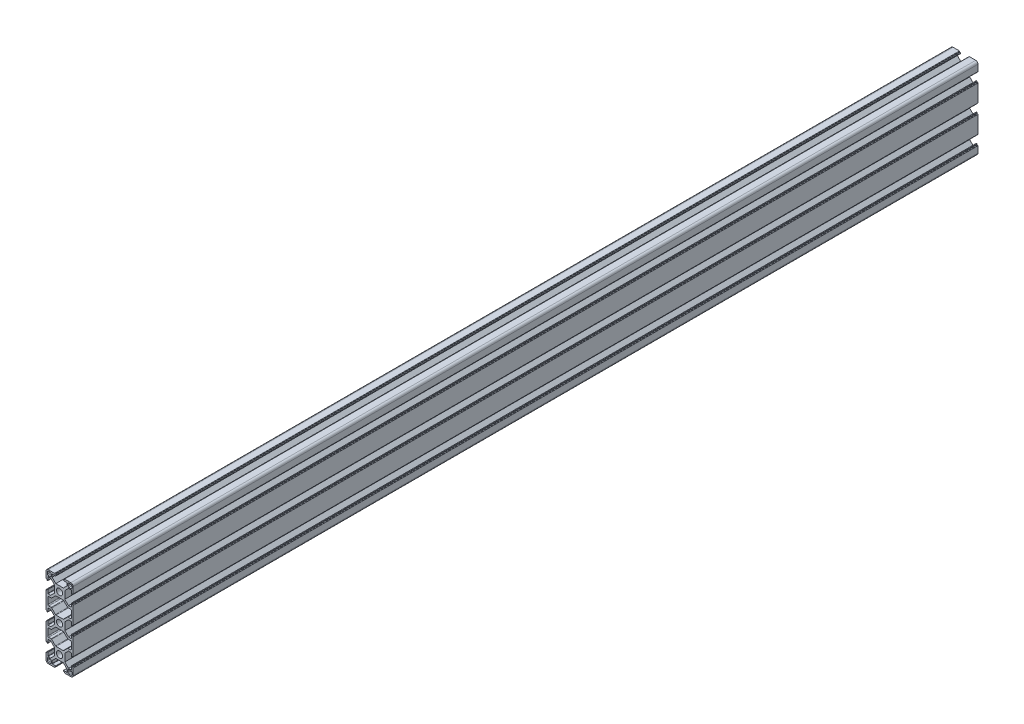
SolidWorks part; units mm, degrees
material "6063 T5"
ref_plane "Спереди" through (0, 0, 0) normal (0, 0, 1) x (1, 0, 0)
ref_plane "Сверху" through (0, 0, 0) normal (0, 1, 0) x (1, 0, 0)
ref_plane "Справа" through (0, 0, 0) normal (1, 0, 0) x (0, 0, -1)
sketch "Эскиз1" plane through (0, 0, 0) normal (0, 0, 1) x (1, 0, 0)
  line L0 (42.4804, 14.8887) -> (42.4804, -45.1113) construction
  line L1 (-15, 8.25) -> (-15, 12.5)
  line L2 (-12.5, 15) -> (-8.25, 15)
  line L3 (8.25, 15) -> (12.5, 15)
  line L4 (15, 12.5) -> (15, 8.25)
  line L5 (12.55, 9.35) -> (10.35, 9.35)
  line L6 (-12.55, 13.55) -> (-10.35, 13.55)
  line L7 (-13.55, 12.55) -> (-13.55, 10.35)
  line L8 (-12.55, 9.35) -> (-10.35, 9.35)
  line L9 (-9.35, 12.55) -> (-9.35, 10.35)
  line L10 (13.55, 12.55) -> (13.55, 10.35)
  line L11 (12.55, 13.55) -> (10.35, 13.55)
  line L12 (9.35, 12.55) -> (9.35, 10.35)
  line L13 (0, 0) -> (0, -30) construction
  line L14 (0, -15) -> (-22.4838, -15) construction
  line L23 (-12, -40.5) -> (-9.4029, -40.5)
  line L24 (-8.6958, -40.2071) -> (-4.5816, -36.0929)
  line L25 (-3.8745, -35.8) -> (3.8745, -35.8)
  line L26 (8.6958, -40.2071) -> (4.5816, -36.0929)
  line L27 (-15, -8.25) -> (-15, -21.75)
  line L28 (15, -8.25) -> (15, -21.75)
  line L29 (-13, -18.5) -> (-13, -11.5)
  line L30 (-12, -10.5) -> (-9.4029, -10.5)
  line L31 (-8.6958, -10.2071) -> (-4.5816, -6.0929)
  line L32 (-3.8745, -5.8) -> (3.8745, -5.8)
  line L33 (8.6958, -10.2071) -> (4.5816, -6.0929)
  line L34 (12, -10.5) -> (9.4029, -10.5)
  line L35 (13, -18.5) -> (13, -11.5)
  line L36 (12, -19.5) -> (9.4029, -19.5)
  line L37 (8.6958, -19.7929) -> (4.5816, -23.9071)
  line L38 (-3.8745, -24.2) -> (3.8745, -24.2)
  line L39 (-8.6958, -19.7929) -> (-4.5816, -23.9071)
  line L40 (-12, -19.5) -> (-9.4029, -19.5)
  line L41 (12, -40.5) -> (9.4029, -40.5)
  line L42 (13, -41.5) -> (13, -48.5)
  line L43 (12, -49.5) -> (9.4029, -49.5)
  line L44 (8.6958, -49.7929) -> (4.5816, -53.9071)
  line L45 (-3.8745, -54.2) -> (3.8745, -54.2)
  line L46 (-8.6958, -49.7929) -> (-4.5816, -53.9071)
  line L47 (-12, -49.5) -> (-9.4029, -49.5)
  line L48 (-13, -41.5) -> (-13, -48.5)
  line L49 (15, -51.75) -> (15, -38.25)
  line L50 (-15, -51.75) -> (-15, -38.25)
  line L51 (9.35, -72.55) -> (9.35, -70.35)
  line L52 (12.55, -73.55) -> (10.35, -73.55)
  line L53 (13.55, -72.55) -> (13.55, -70.35)
  line L54 (-9.35, -72.55) -> (-9.35, -70.35)
  line L55 (-12.55, -69.35) -> (-10.35, -69.35)
  line L56 (-13.55, -72.55) -> (-13.55, -70.35)
  line L57 (-12.55, -73.55) -> (-10.35, -73.55)
  line L58 (12.55, -69.35) -> (10.35, -69.35)
  line L59 (15, -72.5) -> (15, -68.25)
  line L60 (8.25, -75) -> (12.5, -75)
  line L61 (-12.5, -75) -> (-8.25, -75)
  line L62 (-15, -68.25) -> (-15, -72.5)
  arc A0 (12.5, 15) -> (15, 12.5) centre (12.5, 12.5) cw
  arc A1 (-15, 12.5) -> (-12.5, 15) centre (-12.5, 12.5) cw
  arc A2 (-13.55, 10.35) -> (-12.55, 9.35) centre (-12.55, 10.35) ccw
  arc A3 (-10.35, 9.35) -> (-9.35, 10.35) centre (-10.35, 10.35) ccw
  arc A4 (-10.35, 13.55) -> (-9.35, 12.55) centre (-10.35, 12.55) cw
  arc A5 (-12.55, 13.55) -> (-13.55, 12.55) centre (-12.55, 12.55) ccw
  arc A6 (10.35, 9.35) -> (9.35, 10.35) centre (10.35, 10.35) cw
  arc A7 (13.55, 10.35) -> (12.55, 9.35) centre (12.55, 10.35) cw
  arc A8 (12.55, 13.55) -> (13.55, 12.55) centre (12.55, 12.55) cw
  arc A9 (10.35, 13.55) -> (9.35, 12.55) centre (10.35, 12.55) ccw
  circle A10 centre (0, 0) radius 3.4
  circle A11 centre (0, -30) radius 3.4
  arc A20 (-13, -41.5) -> (-12, -40.5) centre (-12, -41.5) cw
  arc A21 (-9.4029, -40.5) -> (-8.6958, -40.2071) centre (-9.4029, -39.5) ccw
  arc A22 (-4.5816, -6.0929) -> (-3.8745, -5.8) centre (-3.8745, -6.8) cw
  arc A23 (-9.4029, -10.5) -> (-8.6958, -10.2071) centre (-9.4029, -9.5) ccw
  arc A24 (-13, -11.5) -> (-12, -10.5) centre (-12, -11.5) cw
  arc A25 (4.5816, -6.0929) -> (3.8745, -5.8) centre (3.8745, -6.8) ccw
  arc A26 (9.4029, -10.5) -> (8.6958, -10.2071) centre (9.4029, -9.5) cw
  arc A27 (13, -11.5) -> (12, -10.5) centre (12, -11.5) ccw
  arc A28 (13, -18.5) -> (12, -19.5) centre (12, -18.5) cw
  arc A29 (9.4029, -19.5) -> (8.6958, -19.7929) centre (9.4029, -20.5) ccw
  arc A30 (4.5816, -23.9071) -> (3.8745, -24.2) centre (3.8745, -23.2) cw
  arc A31 (-4.5816, -23.9071) -> (-3.8745, -24.2) centre (-3.8745, -23.2) ccw
  arc A32 (-9.4029, -19.5) -> (-8.6958, -19.7929) centre (-9.4029, -20.5) cw
  arc A33 (-13, -18.5) -> (-12, -19.5) centre (-12, -18.5) ccw
  arc A34 (-4.5816, -36.0929) -> (-3.8745, -35.8) centre (-3.8745, -36.8) cw
  arc A35 (4.5816, -36.0929) -> (3.8745, -35.8) centre (3.8745, -36.8) ccw
  arc A36 (9.4029, -40.5) -> (8.6958, -40.2071) centre (9.4029, -39.5) cw
  arc A37 (13, -41.5) -> (12, -40.5) centre (12, -41.5) ccw
  arc A38 (13, -48.5) -> (12, -49.5) centre (12, -48.5) cw
  arc A39 (9.4029, -49.5) -> (8.6958, -49.7929) centre (9.4029, -50.5) ccw
  arc A40 (4.5816, -53.9071) -> (3.8745, -54.2) centre (3.8745, -53.2) cw
  arc A41 (-13, -48.5) -> (-12, -49.5) centre (-12, -48.5) ccw
  arc A42 (-9.4029, -49.5) -> (-8.6958, -49.7929) centre (-9.4029, -50.5) cw
  arc A43 (-4.5816, -53.9071) -> (-3.8745, -54.2) centre (-3.8745, -53.2) ccw
  circle A44 centre (0, -60) radius 3.4
  arc A45 (10.35, -73.55) -> (9.35, -72.55) centre (10.35, -72.55) cw
  arc A46 (12.55, -73.55) -> (13.55, -72.55) centre (12.55, -72.55) ccw
  arc A47 (13.55, -70.35) -> (12.55, -69.35) centre (12.55, -70.35) ccw
  arc A48 (10.35, -69.35) -> (9.35, -70.35) centre (10.35, -70.35) ccw
  arc A49 (-12.55, -73.55) -> (-13.55, -72.55) centre (-12.55, -72.55) cw
  arc A50 (-10.35, -73.55) -> (-9.35, -72.55) centre (-10.35, -72.55) ccw
  arc A51 (-10.35, -69.35) -> (-9.35, -70.35) centre (-10.35, -70.35) cw
  arc A52 (-13.55, -70.35) -> (-12.55, -69.35) centre (-12.55, -70.35) cw
  arc A53 (-15, -72.5) -> (-12.5, -75) centre (-12.5, -72.5) ccw
  arc A54 (12.5, -75) -> (15, -72.5) centre (12.5, -72.5) ccw
  point P4 (0, 0)
  point P24 (-9.35, 13.55)
  point P27 (-13.55, 13.55)
  point P77 (0, -30)
  point P100 (0, -5.8)
  point P110 (13, -15)
  point P127 (-13, -15)
  point P166 (-13, -45)
  point P167 (13, -45)
  point P168 (0, -54.2)
  point P169 (-13.55, -73.55)
  point P170 (-9.35, -73.55)
  point P171 (0, -60)
  line B0 (-15, 8.25) -> (-15, 5.5)
  line B1 (-14.7, 5.2) -> (-14.3, 5.2)
  line B2 (-14, 4.9) -> (-14, 4.4)
  line B3 (-13.7, 4.1) -> (-13.3, 4.1)
  line B4 (-13, 4.4) -> (-13, 7.95)
  line B5 (-12.7, 8.25) -> (-9.85, 8.25)
  line B6 (-9.85, 8.25) -> (-5.8, 4.2)
  line B7 (-5.8, 0) -> (-15, 0) construction
  line B8 (-5.8, -4.2) -> (-5.8, 4.2)
  line B9 (-9.85, -8.25) -> (-5.8, -4.2)
  line B10 (-12.7, -8.25) -> (-9.85, -8.25)
  line B11 (-13, -4.4) -> (-13, -7.95)
  line B12 (-13.7, -4.1) -> (-13.3, -4.1)
  line B13 (-14, -4.9) -> (-14, -4.4)
  line B14 (-14.7, -5.2) -> (-14.3, -5.2)
  line B15 (-15, -8.25) -> (-15, -5.5)
  arc B16 (-13, 7.95) -> (-12.7, 8.25) centre (-12.7, 7.95) cw
  arc B17 (-13.3, 4.1) -> (-13, 4.4) centre (-13.3, 4.4) ccw
  arc B18 (-14, 4.4) -> (-13.7, 4.1) centre (-13.7, 4.4) ccw
  arc B19 (-14.3, 5.2) -> (-14, 4.9) centre (-14.3, 4.9) cw
  arc B20 (-15, 5.5) -> (-14.7, 5.2) centre (-14.7, 5.5) ccw
  arc B21 (-15, -5.5) -> (-14.7, -5.2) centre (-14.7, -5.5) cw
  arc B22 (-14.3, -5.2) -> (-14, -4.9) centre (-14.3, -4.9) ccw
  arc B23 (-14, -4.4) -> (-13.7, -4.1) centre (-13.7, -4.4) cw
  arc B24 (-13.3, -4.1) -> (-13, -4.4) centre (-13.3, -4.4) cw
  arc B25 (-13, -7.95) -> (-12.7, -8.25) centre (-12.7, -7.95) ccw
  line B26 (8.25, 15) -> (5.5, 15)
  line B27 (5.2, 14.7) -> (5.2, 14.3)
  line B28 (4.9, 14) -> (4.4, 14)
  line B29 (4.1, 13.7) -> (4.1, 13.3)
  line B30 (4.4, 13) -> (7.95, 13)
  line B31 (8.25, 12.7) -> (8.25, 9.85)
  line B32 (8.25, 9.85) -> (4.2, 5.8)
  line B33 (0, 5.8) -> (0, 15) construction
  line B34 (-4.2, 5.8) -> (4.2, 5.8)
  line B35 (-8.25, 9.85) -> (-4.2, 5.8)
  line B36 (-8.25, 12.7) -> (-8.25, 9.85)
  line B37 (-4.4, 13) -> (-7.95, 13)
  line B38 (-4.1, 13.7) -> (-4.1, 13.3)
  line B39 (-4.9, 14) -> (-4.4, 14)
  line B40 (-5.2, 14.7) -> (-5.2, 14.3)
  line B41 (-8.25, 15) -> (-5.5, 15)
  arc B42 (7.95, 13) -> (8.25, 12.7) centre (7.95, 12.7) cw
  arc B43 (4.1, 13.3) -> (4.4, 13) centre (4.4, 13.3) ccw
  arc B44 (4.4, 14) -> (4.1, 13.7) centre (4.4, 13.7) ccw
  arc B45 (5.2, 14.3) -> (4.9, 14) centre (4.9, 14.3) cw
  arc B46 (5.5, 15) -> (5.2, 14.7) centre (5.5, 14.7) ccw
  arc B47 (-5.5, 15) -> (-5.2, 14.7) centre (-5.5, 14.7) cw
  arc B48 (-5.2, 14.3) -> (-4.9, 14) centre (-4.9, 14.3) ccw
  arc B49 (-4.4, 14) -> (-4.1, 13.7) centre (-4.4, 13.7) cw
  arc B50 (-4.1, 13.3) -> (-4.4, 13) centre (-4.4, 13.3) cw
  arc B51 (-7.95, 13) -> (-8.25, 12.7) centre (-7.95, 12.7) ccw
  line B52 (15, -8.25) -> (15, -5.5)
  line B53 (14.7, -5.2) -> (14.3, -5.2)
  line B54 (14, -4.9) -> (14, -4.4)
  line B55 (13.7, -4.1) -> (13.3, -4.1)
  line B56 (13, -4.4) -> (13, -7.95)
  line B57 (12.7, -8.25) -> (9.85, -8.25)
  line B58 (9.85, -8.25) -> (5.8, -4.2)
  line B59 (5.8, 0) -> (15, 0) construction
  line B60 (5.8, 4.2) -> (5.8, -4.2)
  line B61 (9.85, 8.25) -> (5.8, 4.2)
  line B62 (12.7, 8.25) -> (9.85, 8.25)
  line B63 (13, 4.4) -> (13, 7.95)
  line B64 (13.7, 4.1) -> (13.3, 4.1)
  line B65 (14, 4.9) -> (14, 4.4)
  line B66 (14.7, 5.2) -> (14.3, 5.2)
  line B67 (15, 8.25) -> (15, 5.5)
  arc B68 (13, -7.95) -> (12.7, -8.25) centre (12.7, -7.95) cw
  arc B69 (13.3, -4.1) -> (13, -4.4) centre (13.3, -4.4) ccw
  arc B70 (14, -4.4) -> (13.7, -4.1) centre (13.7, -4.4) ccw
  arc B71 (14.3, -5.2) -> (14, -4.9) centre (14.3, -4.9) cw
  arc B72 (15, -5.5) -> (14.7, -5.2) centre (14.7, -5.5) ccw
  arc B73 (15, 5.5) -> (14.7, 5.2) centre (14.7, 5.5) cw
  arc B74 (14.3, 5.2) -> (14, 4.9) centre (14.3, 4.9) ccw
  arc B75 (14, 4.4) -> (13.7, 4.1) centre (13.7, 4.4) cw
  arc B76 (13.3, 4.1) -> (13, 4.4) centre (13.3, 4.4) cw
  arc B77 (13, 7.95) -> (12.7, 8.25) centre (12.7, 7.95) ccw
  line B78 (-15, -38.25) -> (-15, -35.5)
  line B79 (-14.7, -35.2) -> (-14.3, -35.2)
  line B80 (-14, -34.9) -> (-14, -34.4)
  line B81 (-13.7, -34.1) -> (-13.3, -34.1)
  line B82 (-13, -34.4) -> (-13, -37.95)
  line B83 (-12.7, -38.25) -> (-9.85, -38.25)
  line B84 (-9.85, -38.25) -> (-5.8, -34.2)
  line B85 (-5.8, -30) -> (-15, -30) construction
  line B86 (-5.8, -25.8) -> (-5.8, -34.2)
  line B87 (-9.85, -21.75) -> (-5.8, -25.8)
  line B88 (-12.7, -21.75) -> (-9.85, -21.75)
  line B89 (-13, -25.6) -> (-13, -22.05)
  line B90 (-13.7, -25.9) -> (-13.3, -25.9)
  line B91 (-14, -25.1) -> (-14, -25.6)
  line B92 (-14.7, -24.8) -> (-14.3, -24.8)
  line B93 (-15, -21.75) -> (-15, -24.5)
  arc B94 (-13, -37.95) -> (-12.7, -38.25) centre (-12.7, -37.95) ccw
  arc B95 (-13.3, -34.1) -> (-13, -34.4) centre (-13.3, -34.4) cw
  arc B96 (-14, -34.4) -> (-13.7, -34.1) centre (-13.7, -34.4) cw
  arc B97 (-14.3, -35.2) -> (-14, -34.9) centre (-14.3, -34.9) ccw
  arc B98 (-15, -35.5) -> (-14.7, -35.2) centre (-14.7, -35.5) cw
  arc B99 (-15, -24.5) -> (-14.7, -24.8) centre (-14.7, -24.5) ccw
  arc B100 (-14.3, -24.8) -> (-14, -25.1) centre (-14.3, -25.1) cw
  arc B101 (-14, -25.6) -> (-13.7, -25.9) centre (-13.7, -25.6) ccw
  arc B102 (-13.3, -25.9) -> (-13, -25.6) centre (-13.3, -25.6) ccw
  arc B103 (-13, -22.05) -> (-12.7, -21.75) centre (-12.7, -22.05) cw
  line B104 (15, -21.75) -> (15, -24.5)
  line B105 (14.7, -24.8) -> (14.3, -24.8)
  line B106 (14, -25.1) -> (14, -25.6)
  line B107 (13.7, -25.9) -> (13.3, -25.9)
  line B108 (13, -25.6) -> (13, -22.05)
  line B109 (12.7, -21.75) -> (9.85, -21.75)
  line B110 (9.85, -21.75) -> (5.8, -25.8)
  line B111 (5.8, -30) -> (15, -30) construction
  line B112 (5.8, -34.2) -> (5.8, -25.8)
  line B113 (9.85, -38.25) -> (5.8, -34.2)
  line B114 (12.7, -38.25) -> (9.85, -38.25)
  line B115 (13, -34.4) -> (13, -37.95)
  line B116 (13.7, -34.1) -> (13.3, -34.1)
  line B117 (14, -34.9) -> (14, -34.4)
  line B118 (14.7, -35.2) -> (14.3, -35.2)
  line B119 (15, -38.25) -> (15, -35.5)
  arc B120 (13, -22.05) -> (12.7, -21.75) centre (12.7, -22.05) ccw
  arc B121 (13.3, -25.9) -> (13, -25.6) centre (13.3, -25.6) cw
  arc B122 (14, -25.6) -> (13.7, -25.9) centre (13.7, -25.6) cw
  arc B123 (14.3, -24.8) -> (14, -25.1) centre (14.3, -25.1) ccw
  arc B124 (15, -24.5) -> (14.7, -24.8) centre (14.7, -24.5) cw
  arc B125 (15, -35.5) -> (14.7, -35.2) centre (14.7, -35.5) ccw
  arc B126 (14.3, -35.2) -> (14, -34.9) centre (14.3, -34.9) cw
  arc B127 (14, -34.4) -> (13.7, -34.1) centre (13.7, -34.4) ccw
  arc B128 (13.3, -34.1) -> (13, -34.4) centre (13.3, -34.4) ccw
  arc B129 (13, -37.95) -> (12.7, -38.25) centre (12.7, -37.95) cw
  line B130 (-15, -68.25) -> (-15, -65.5)
  line B131 (-14.7, -65.2) -> (-14.3, -65.2)
  line B132 (-14, -64.9) -> (-14, -64.4)
  line B133 (-13.7, -64.1) -> (-13.3, -64.1)
  line B134 (-13, -64.4) -> (-13, -67.95)
  line B135 (-12.7, -68.25) -> (-9.85, -68.25)
  line B136 (-9.85, -68.25) -> (-5.8, -64.2)
  line B137 (-5.8, -60) -> (-15, -60) construction
  line B138 (-5.8, -55.8) -> (-5.8, -64.2)
  line B139 (-9.85, -51.75) -> (-5.8, -55.8)
  line B140 (-12.7, -51.75) -> (-9.85, -51.75)
  line B141 (-13, -55.6) -> (-13, -52.05)
  line B142 (-13.7, -55.9) -> (-13.3, -55.9)
  line B143 (-14, -55.1) -> (-14, -55.6)
  line B144 (-14.7, -54.8) -> (-14.3, -54.8)
  line B145 (-15, -51.75) -> (-15, -54.5)
  arc B146 (-13, -67.95) -> (-12.7, -68.25) centre (-12.7, -67.95) ccw
  arc B147 (-13.3, -64.1) -> (-13, -64.4) centre (-13.3, -64.4) cw
  arc B148 (-14, -64.4) -> (-13.7, -64.1) centre (-13.7, -64.4) cw
  arc B149 (-14.3, -65.2) -> (-14, -64.9) centre (-14.3, -64.9) ccw
  arc B150 (-15, -65.5) -> (-14.7, -65.2) centre (-14.7, -65.5) cw
  arc B151 (-15, -54.5) -> (-14.7, -54.8) centre (-14.7, -54.5) ccw
  arc B152 (-14.3, -54.8) -> (-14, -55.1) centre (-14.3, -55.1) cw
  arc B153 (-14, -55.6) -> (-13.7, -55.9) centre (-13.7, -55.6) ccw
  arc B154 (-13.3, -55.9) -> (-13, -55.6) centre (-13.3, -55.6) ccw
  arc B155 (-13, -52.05) -> (-12.7, -51.75) centre (-12.7, -52.05) cw
  line B156 (15, -51.75) -> (15, -54.5)
  line B157 (14.7, -54.8) -> (14.3, -54.8)
  line B158 (14, -55.1) -> (14, -55.6)
  line B159 (13.7, -55.9) -> (13.3, -55.9)
  line B160 (13, -55.6) -> (13, -52.05)
  line B161 (12.7, -51.75) -> (9.85, -51.75)
  line B162 (9.85, -51.75) -> (5.8, -55.8)
  line B163 (5.8, -60) -> (15, -60) construction
  line B164 (5.8, -64.2) -> (5.8, -55.8)
  line B165 (9.85, -68.25) -> (5.8, -64.2)
  line B166 (12.7, -68.25) -> (9.85, -68.25)
  line B167 (13, -64.4) -> (13, -67.95)
  line B168 (13.7, -64.1) -> (13.3, -64.1)
  line B169 (14, -64.9) -> (14, -64.4)
  line B170 (14.7, -65.2) -> (14.3, -65.2)
  line B171 (15, -68.25) -> (15, -65.5)
  arc B172 (13, -52.05) -> (12.7, -51.75) centre (12.7, -52.05) ccw
  arc B173 (13.3, -55.9) -> (13, -55.6) centre (13.3, -55.6) cw
  arc B174 (14, -55.6) -> (13.7, -55.9) centre (13.7, -55.6) cw
  arc B175 (14.3, -54.8) -> (14, -55.1) centre (14.3, -55.1) ccw
  arc B176 (15, -54.5) -> (14.7, -54.8) centre (14.7, -54.5) cw
  arc B177 (15, -65.5) -> (14.7, -65.2) centre (14.7, -65.5) ccw
  arc B178 (14.3, -65.2) -> (14, -64.9) centre (14.3, -64.9) cw
  arc B179 (14, -64.4) -> (13.7, -64.1) centre (13.7, -64.4) ccw
  arc B180 (13.3, -64.1) -> (13, -64.4) centre (13.3, -64.4) ccw
  arc B181 (13, -67.95) -> (12.7, -68.25) centre (12.7, -67.95) cw
  line B182 (-15, -21.75) -> (-15, -24.5)
  line B183 (-14.7, -24.8) -> (-14.3, -24.8)
  line B184 (-14, -25.1) -> (-14, -25.6)
  line B185 (-13.7, -25.9) -> (-13.3, -25.9)
  line B186 (-13, -25.6) -> (-13, -22.05)
  line B187 (-12.7, -21.75) -> (-9.85, -21.75)
  line B188 (-9.85, -21.75) -> (-5.8, -25.8)
  line B189 (-5.8, -30) -> (-15, -30) construction
  line B190 (-5.8, -34.2) -> (-5.8, -25.8)
  line B191 (-9.85, -38.25) -> (-5.8, -34.2)
  line B192 (-12.7, -38.25) -> (-9.85, -38.25)
  line B193 (-13, -34.4) -> (-13, -37.95)
  line B194 (-13.7, -34.1) -> (-13.3, -34.1)
  line B195 (-14, -34.9) -> (-14, -34.4)
  line B196 (-14.7, -35.2) -> (-14.3, -35.2)
  line B197 (-15, -38.25) -> (-15, -35.5)
  arc B198 (-13, -22.05) -> (-12.7, -21.75) centre (-12.7, -22.05) cw
  arc B199 (-13.3, -25.9) -> (-13, -25.6) centre (-13.3, -25.6) ccw
  arc B200 (-14, -25.6) -> (-13.7, -25.9) centre (-13.7, -25.6) ccw
  arc B201 (-14.3, -24.8) -> (-14, -25.1) centre (-14.3, -25.1) cw
  arc B202 (-15, -24.5) -> (-14.7, -24.8) centre (-14.7, -24.5) ccw
  arc B203 (-15, -35.5) -> (-14.7, -35.2) centre (-14.7, -35.5) cw
  arc B204 (-14.3, -35.2) -> (-14, -34.9) centre (-14.3, -34.9) ccw
  arc B205 (-14, -34.4) -> (-13.7, -34.1) centre (-13.7, -34.4) cw
  arc B206 (-13.3, -34.1) -> (-13, -34.4) centre (-13.3, -34.4) cw
  arc B207 (-13, -37.95) -> (-12.7, -38.25) centre (-12.7, -37.95) ccw
  line B208 (8.25, -75) -> (5.5, -75)
  line B209 (5.2, -74.7) -> (5.2, -74.3)
  line B210 (4.9, -74) -> (4.4, -74)
  line B211 (4.1, -73.7) -> (4.1, -73.3)
  line B212 (4.4, -73) -> (7.95, -73)
  line B213 (8.25, -72.7) -> (8.25, -69.85)
  line B214 (8.25, -69.85) -> (4.2, -65.8)
  line B215 (0, -65.8) -> (0, -75) construction
  line B216 (-4.2, -65.8) -> (4.2, -65.8)
  line B217 (-8.25, -69.85) -> (-4.2, -65.8)
  line B218 (-8.25, -72.7) -> (-8.25, -69.85)
  line B219 (-4.4, -73) -> (-7.95, -73)
  line B220 (-4.1, -73.7) -> (-4.1, -73.3)
  line B221 (-4.9, -74) -> (-4.4, -74)
  line B222 (-5.2, -74.7) -> (-5.2, -74.3)
  line B223 (-8.25, -75) -> (-5.5, -75)
  arc B224 (7.95, -73) -> (8.25, -72.7) centre (7.95, -72.7) ccw
  arc B225 (4.1, -73.3) -> (4.4, -73) centre (4.4, -73.3) cw
  arc B226 (4.4, -74) -> (4.1, -73.7) centre (4.4, -73.7) cw
  arc B227 (5.2, -74.3) -> (4.9, -74) centre (4.9, -74.3) ccw
  arc B228 (5.5, -75) -> (5.2, -74.7) centre (5.5, -74.7) cw
  arc B229 (-5.5, -75) -> (-5.2, -74.7) centre (-5.5, -74.7) ccw
  arc B230 (-5.2, -74.3) -> (-4.9, -74) centre (-4.9, -74.3) cw
  arc B231 (-4.4, -74) -> (-4.1, -73.7) centre (-4.4, -73.7) ccw
  arc B232 (-4.1, -73.3) -> (-4.4, -73) centre (-4.4, -73.3) ccw
  arc B233 (-7.95, -73) -> (-8.25, -72.7) centre (-7.95, -72.7) cw
  line B234 (15, -38.25) -> (15, -35.5)
  line B235 (14.7, -35.2) -> (14.3, -35.2)
  line B236 (14, -34.9) -> (14, -34.4)
  line B237 (13.7, -34.1) -> (13.3, -34.1)
  line B238 (13, -34.4) -> (13, -37.95)
  line B239 (12.7, -38.25) -> (9.85, -38.25)
  line B240 (9.85, -38.25) -> (5.8, -34.2)
  line B241 (5.8, -30) -> (15, -30) construction
  line B242 (5.8, -25.8) -> (5.8, -34.2)
  line B243 (9.85, -21.75) -> (5.8, -25.8)
  line B244 (12.7, -21.75) -> (9.85, -21.75)
  line B245 (13, -25.6) -> (13, -22.05)
  line B246 (13.7, -25.9) -> (13.3, -25.9)
  line B247 (14, -25.1) -> (14, -25.6)
  line B248 (14.7, -24.8) -> (14.3, -24.8)
  line B249 (15, -21.75) -> (15, -24.5)
  arc B250 (13, -37.95) -> (12.7, -38.25) centre (12.7, -37.95) cw
  arc B251 (13.3, -34.1) -> (13, -34.4) centre (13.3, -34.4) ccw
  arc B252 (14, -34.4) -> (13.7, -34.1) centre (13.7, -34.4) ccw
  arc B253 (14.3, -35.2) -> (14, -34.9) centre (14.3, -34.9) cw
  arc B254 (15, -35.5) -> (14.7, -35.2) centre (14.7, -35.5) ccw
  arc B255 (15, -24.5) -> (14.7, -24.8) centre (14.7, -24.5) cw
  arc B256 (14.3, -24.8) -> (14, -25.1) centre (14.3, -25.1) ccw
  arc B257 (14, -25.6) -> (13.7, -25.9) centre (13.7, -25.6) cw
  arc B258 (13.3, -25.9) -> (13, -25.6) centre (13.3, -25.6) cw
  arc B259 (13, -22.05) -> (12.7, -21.75) centre (12.7, -22.05) ccw
  dimension "D8" = 6.8
  dimension "D3" = 2.5
  dimension "D7" = 1
  dimension "D14" = 1
  dimension "D1" = 15
  dimension "D2" = 60
  dimension "D4" = 1.1
  dimension "D5" = 1.1
  dimension "D6" = 4.2
  dimension "D9" = 30
  dimension "D10" = 9
  dimension "D11" = 26
  dimension "D12" = 18.4
  dimension "D13" = 2.2
sketch_block_instance "Блок1-1"
sketch_block "Блок1" parameters "D6"=0.3, "D1"=16.5, "D2"=8.4, "D3"=9.2, "D4"=45, "D5"=10.4, "D7"=2, "D8"=1, "D9"=8.2
sketch_block_instance "Блок1-2"
sketch_block_instance "Блок1-3"
sketch_block_instance "Блок1-5"
sketch_block_instance "Блок1-6"
sketch_block_instance "Блок1-12"
sketch_block_instance "Блок1-13"
sketch_block_instance "Блок1-14"
sketch_block_instance "Блок1-15"
sketch_block_instance "Блок1-16"
extrude "Бобышка-Вытянуть1" add sketch "Эскиз1" along normal blind 1000 contours B115 B129 B114 B113 B112 B110 B109 B120 B108 B121 B107 B122 B106 B123 B105 B124 B104 L28 B52 B72 B53 B71 B54 B70 B55 B69 B56 B68 B57 B58 B60 B61 B62 B77 B63 B76 B64 B75 B65 B74 B66 B73 B67 L4 A0 L3 B26 B46 B27 B45 B28
